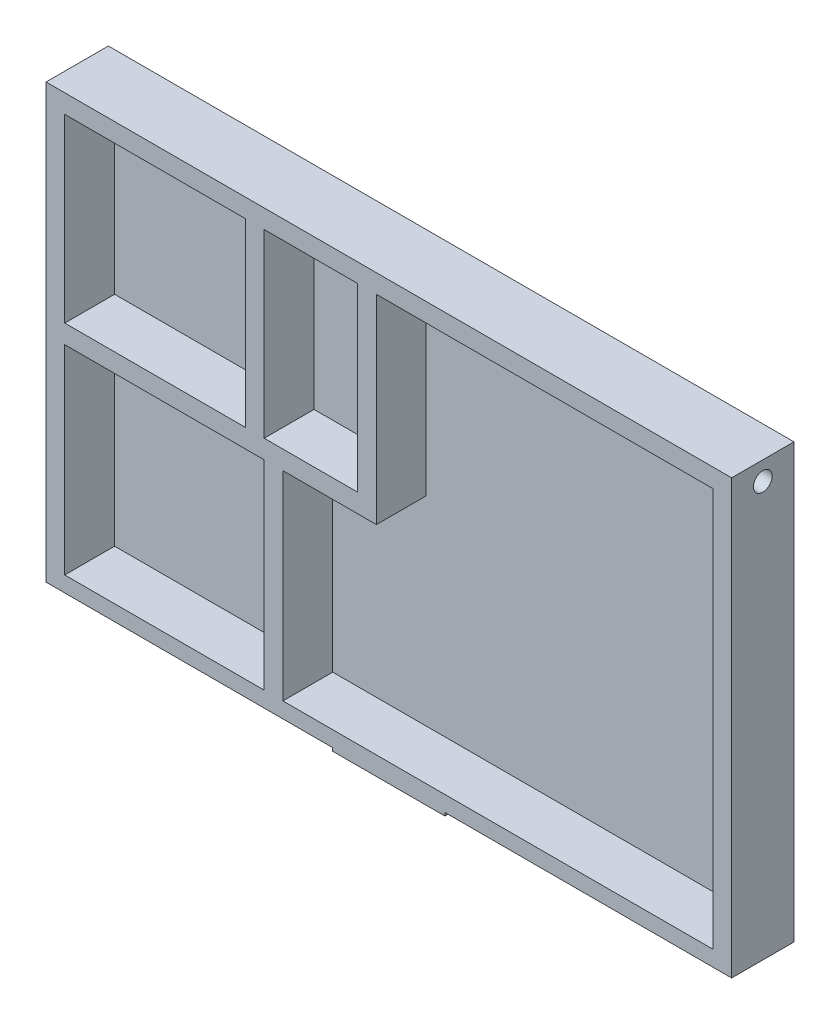
SolidWorks part; units mm, degrees
ref_plane "Front Plane" through (0, 0, 0) normal (0, 0, 1) x (1, 0, 0)
ref_plane "Top Plane" through (0, 0, 0) normal (0, 1, 0) x (1, 0, 0)
ref_plane "Right Plane" through (0, 0, 0) normal (1, 0, 0) x (0, 0, -1)
sketch "Sketch1" plane through (0, 0, 0) normal (0, 0, 1) x (1, 0, 0)
  line L0 (-55, 0) -> (55, 0) construction
  line L1 (-55, -35) -> (55, -35)
  line L2 (-55, -35) -> (-55, 35)
  line L3 (-55, 35) -> (55, 35)
  line L4 (55, -35) -> (55, 35)
  dimension "D1" = 70
  dimension "D2" = 110
extrude "Boss-Extrude1" add sketch "Sketch1" along normal blind 10
sketch "Sketch2" plane through (0, 0, 10) normal (0, 0, 1) x (1, 0, 0)
  line L0 (-55, 35) -> (-55, -35) construction
  line L1 (-52, 32) -> (-23, 32)
  line L2 (-52, 32) -> (-52, 3)
  line L3 (-52, 3) -> (-23, 3)
  line L4 (-23, 32) -> (-23, 3)
  line L5 (-52, 0) -> (-20, 0)
  line L6 (-52, 0) -> (-52, -32)
  line L7 (-52, -32) -> (-20, -32)
  line L8 (-20, 0) -> (-20, -32)
  line L9 (-20, 32) -> (-5, 32)
  line L10 (-20, 32) -> (-20, 3)
  line L11 (-20, 3) -> (-5, 3)
  line L12 (-5, 32) -> (-5, 3)
  line L13 (55, 35) -> (-55, 35) construction
  line L14 (-55, -35) -> (55, -35) construction
  dimension "D1" = 3
  dimension "D2" = 3
  dimension "D4" = 15
  dimension "D5" = 3
  dimension "D6" = 3
  dimension "D7" = 3
extrude "Cut-Extrude1" cut sketch "Sketch2" against normal blind 8
sketch "Sketch3" plane through (0, 0, 10) normal (0, 0, 1) x (1, 0, 0)
  line L0 (-17, -32) -> (52, -32)
  line L1 (52, -32) -> (52, 32)
  line L2 (52, 32) -> (-2, 32)
  line L4 (-55, 35) -> (-55, -35)
  line L5 (-55, -35) -> (55, -35)
  line L6 (55, -35) -> (55, 35)
  line L7 (55, 35) -> (-55, 35)
  line L8 (-55, 35) -> (-55, -35)
  line L9 (-55, -35) -> (55, -35)
  line L10 (55, -35) -> (55, 35)
  line L11 (55, 35) -> (-55, 35)
  line L16 (-17, -35) -> (-17, 0)
  line L17 (-17, 0) -> (-2, 0)
  line L18 (-2, 0) -> (-2, 35)
  line L20 (-52, 0) -> (-52, -32)
  line L21 (-52, -32) -> (-20, -32)
  line L22 (-20, -32) -> (-20, 0)
  line L23 (-20, 0) -> (-52, 0)
  line L24 (-52, 0) -> (-52, -32)
  line L25 (-52, -32) -> (-20, -32)
  line L26 (-20, -32) -> (-20, 0)
  line L27 (-20, 0) -> (-52, 0)
  line L28 (-52, 32) -> (-52, 3)
  line L29 (-52, 3) -> (-23, 3)
  line L30 (-23, 3) -> (-23, 32)
  line L31 (-23, 32) -> (-52, 32)
  line L32 (-52, 32) -> (-52, 3)
  line L33 (-52, 3) -> (-23, 3)
  line L34 (-23, 3) -> (-23, 32)
  line L35 (-23, 32) -> (-52, 32)
  line L36 (-20, 32) -> (-20, 3)
  line L37 (-20, 3) -> (-5, 3)
  line L38 (-5, 3) -> (-5, 32)
  line L39 (-5, 32) -> (-20, 32)
  line L40 (-20, 32) -> (-20, 3)
  line L41 (-20, 3) -> (-5, 3)
  line L42 (-5, 3) -> (-5, 32)
  line L43 (-5, 32) -> (-20, 32)
  dimension "D7" = 3
  dimension "D5" = 3
  dimension "D6" = 3
  dimension "D1" = 0
  dimension "D2" = 0
  dimension "D3" = 0
  dimension "D4" = 0
extrude "Cut-Extrude3" cut sketch "Sketch3" against normal blind 8 contours L18 L17 L16 L0 L1 L2
sketch "Sketch4" plane through (-55, 0, 0) normal (-1, 0, 0) x (0, 0, 1)
  line L0 (10, 35) -> (0, 35) construction
  circle A0 centre (5, 32) radius 1.5
  point P4 (5, 35)
  dimension "D1" = 3
  dimension "D2" = 3
extrude "Cut-Extrude4" cut sketch "Sketch4" against normal blind 2.5
ref_plane "Plane1" through (0, 0, 0) normal (-1, 0, 0) x (0, 0, 1)
mirror "Mirror1" about plane through (0, 0, 0) normal (-1, 0, 0) of "Cut-Extrude4"
sketch "Sketch5" plane through (0, 0, 10) normal (0, 0, 1) x (1, 0, 0)
  line L0 (55, -35) -> (55, 35) construction
  line L1 (-55, -35) -> (55, -35)
  line L2 (-55, -35) -> (-55, -34.5)
  line L3 (-55, -34.5) -> (55, -34.5)
  line L4 (55, -35) -> (55, -34.5)
  line L5 (0, 5.5) -> (0, -5.5) construction
  line L6 (-9, -34.5) -> (9, -34.5)
  line L7 (-9, -34.5) -> (-9, -35)
  line L8 (-9, -35) -> (9, -35)
  line L9 (9, -34.5) -> (9, -35)
  point P11 (0, -34.5)
  point P14 (9, -34.75)
  line M3 (-55, 35) -> (-55, -35)
  line M4 (-55, -35) -> (55, -35)
  line M5 (55, -35) -> (55, 35)
  dimension "D1" = 0.5
  dimension "D2" = 18
extrude "Cut-Extrude5" cut sketch "Sketch5" against normal through all contours L7 L3 M3 M4 | L3 L9 M4 M5
sketch "Sketch7" plane through (0, -35, 0) normal (0, -1, 0) x (1, 0, 0)
  line L0 (9, 0) -> (9, 10) construction
  line L1 (-9, 0) -> (9, 0)
  line L2 (-9, 0) -> (-9, 2)
  line L3 (-9, 2) -> (9, 2)
  line L4 (9, 0) -> (9, 2)
  dimension "D1" = 2
extrude "Boss-Extrude2" add sketch "Sketch7" along normal blind 3
